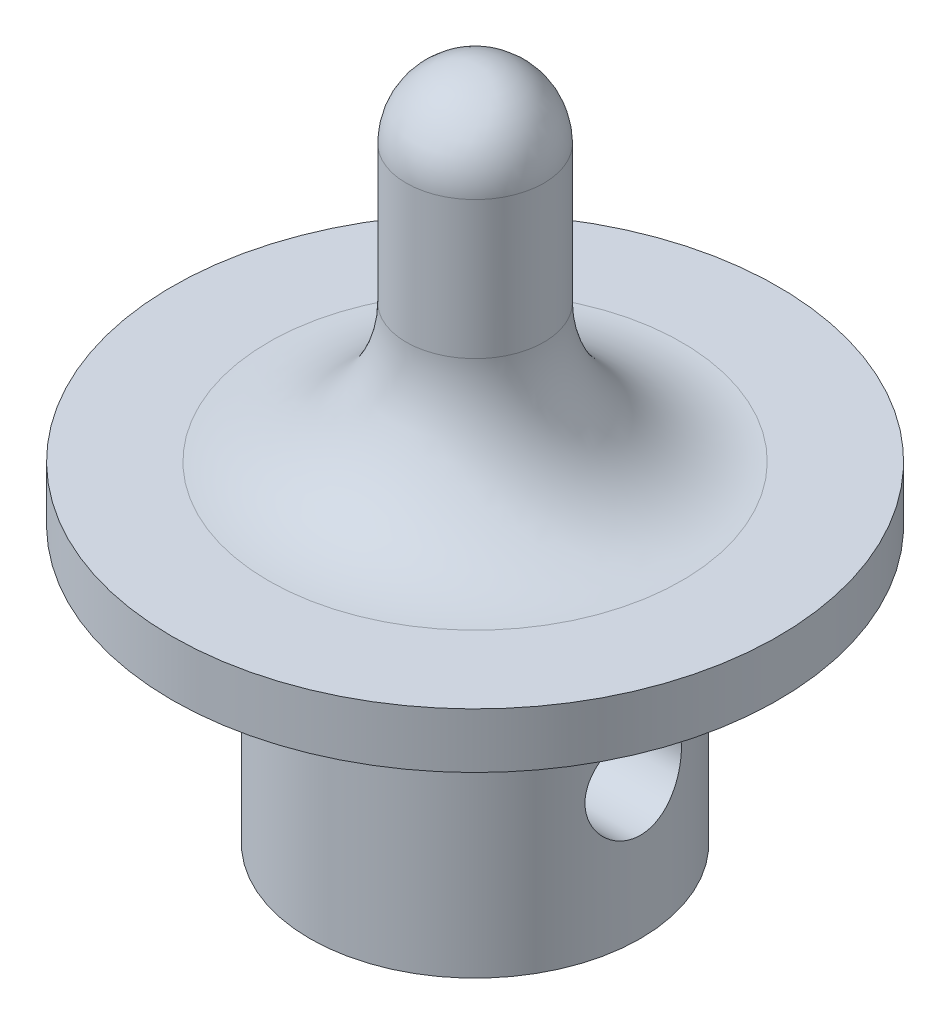
SolidWorks part; units mm, degrees
ref_plane "Front Plane" through (0, 0, 0) normal (0, 0, 1) x (1, 0, 0)
ref_plane "Top Plane" through (0, 0, 0) normal (0, 1, 0) x (1, 0, 0)
ref_plane "Right Plane" through (0, 0, 0) normal (1, 0, 0) x (0, 0, -1)
sketch "Sketch1" plane through (0, 0, 0) normal (0, 1, 0) x (1, 0, 0)
  circle A0 centre (0, 0) radius 6
  dimension "D1" = 12
extrude "Boss-Extrude1" add sketch "Sketch1" along normal blind 10
sketch "Sketch2" plane through (0, 10, 0) normal (0, 1, 0) x (1, 0, 0)
  circle A2 centre (0, 0) radius 11
  circle A3 centre (0, 0) radius 11
  dimension "D1" = 5
extrude "Boss-Extrude2" add sketch "Sketch2" along normal blind 2
sketch "Sketch3" plane through (0, 0, 0) normal (1, 0, 0) x (0, 0, -1)
  line L0 (0, 12) -> (-2.5, 12)
  line L1 (11, 12) -> (-11, 12) construction
  line L2 (-2.5, 12) -> (-2.5, 22)
  line L3 (0, 24.5) -> (0, 12)
  arc A0 (-2.5, 22) -> (0, 24.5) centre (0, 22) cw
  point P7 (0, 0)
  dimension "D1" = 2.5
  dimension "D2" = 10
revolve "Revolve1" add sketch "Sketch3" angle 360 about L3
fillet "Fillet1" radius 5 1 edges at (0, 12, 2.5)
sketch "Sketch5" plane through (0, 0, 0) normal (1, 0, 0) x (0, 0, -1)
  circle A0 centre (0, 5) radius 1.75
  dimension "D1" = 3.5
  dimension "D2" = 5
extrude "Cut-Extrude1" cut sketch "Sketch5" against normal through all both and the other way through all
